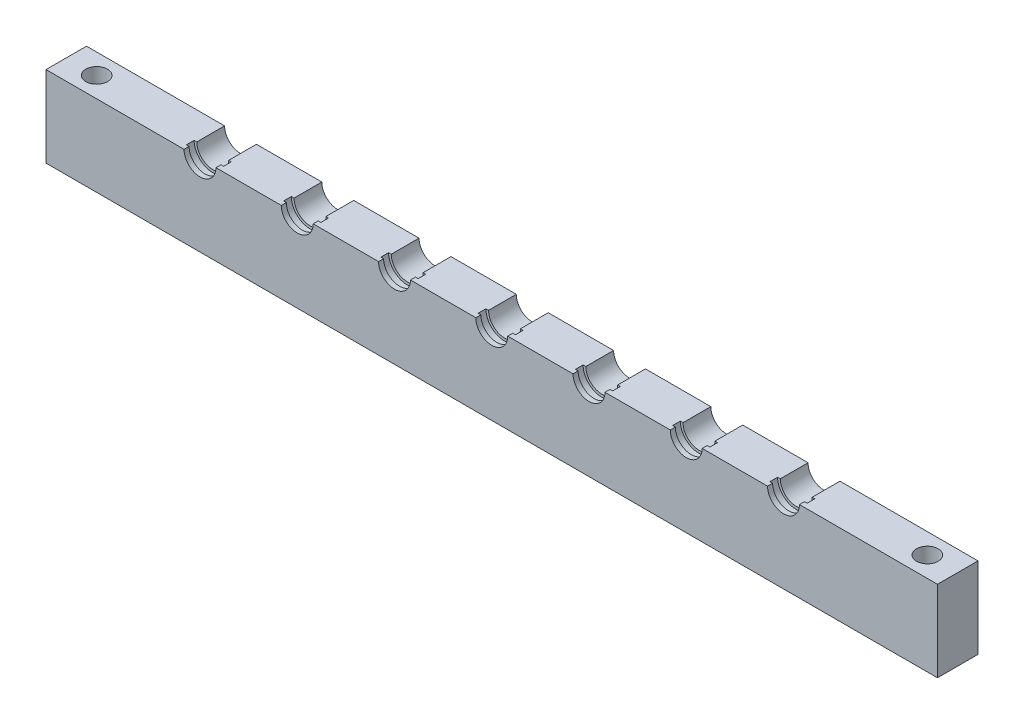
SolidWorks part; units mm, degrees
ref_plane "Front Plane" through (0, 0, 0) normal (0, 0, 1) x (1, 0, 0)
ref_plane "Top Plane" through (0, 0, 0) normal (0, 1, 0) x (1, 0, 0)
ref_plane "Right Plane" through (0, 0, 0) normal (1, 0, 0) x (0, 0, -1)
sketch "Sketch1" plane through (0, 0, 0) normal (0, 0, 1) x (1, 0, 0)
  line L1 (69.85, -6.35) -> (-69.85, -6.35)
  line L2 (69.85, -6.35) -> (69.85, 6.35)
  line L3 (69.85, 6.35) -> (-69.85, 6.35)
  line L4 (-69.85, -6.35) -> (-69.85, 6.35)
  line L5 (69.85, -6.35) -> (-69.85, 6.35) construction
  line L6 (69.85, 6.35) -> (-69.85, -6.35) construction
  point P0 (0, 0)
  dimension "D1" = 139.7
  dimension "D2" = 12.7
extrude "Boss-Extrude1" add sketch "Sketch1" along normal blind 6.35
hole_wizard "M3 Clearance Hole1" positions "Sketch3" profile "Sketch4" hole size "M3" standard "ANSI Metric" end condition through all
sketch "Sketch3" plane through (0, -6.35, 0) normal (0, -1, 0) x (-1, 0, 0)
  line L0 (69.85, -3.175) -> (-69.85, -3.175) construction
  line L1 (69.85, -6.35) -> (69.85, 0) construction
  line L2 (-69.85, -6.35) -> (-69.85, 0) construction
  point P9 (65.0875, -3.175)
  dimension "D1" = 4.7625
sketch "Sketch4" plane through (-65.0875, -6.35, 3.175) normal (1, 0, 0) x (0, 0, -1)
  line L0 (0, 0) -> (0, 12.7)
  line L1 (0, 12.7) -> (1.7, 12.7)
  line L2 (1.7, 12.7) -> (1.7, 0)
  line L5 (1.7, 0) -> (0, 0)
  line L11 (0, -6.35) -> (0, 107.95) construction
  dimension "Thru Hole Dia." = 3.4
  dimension "Thru Hole Depth" = 12.7
mirror "Mirror1" about plane through (0, 0, 0) normal (1, 0, 0) of "M3 Clearance Hole1"
sketch "Sketch9" plane through (0, 6.35, 0) normal (0, 1, 0) x (1, 0, 0)
  line L0 (2.5, -5.5563) -> (2.921, -5.5563) construction
  line L1 (2.5, -6.35) -> (2.5, -5.5563) construction
  line L2 (2.921, -5.5563) -> (2.921, -4.3498) construction
  line L3 (2.5, -4.3498) -> (2.921, -4.3498) construction
  line L4 (2.5, -4.3498) -> (2.5, 0) construction
  line L5 (2.5, -5.5563) -> (2.921, -5.5563)
  line L6 (2.5, -6.35) -> (2.5, -5.5563)
  line L7 (2.921, -5.5563) -> (2.921, -4.3498)
  line L8 (2.5, -4.3498) -> (2.921, -4.3498)
  line L9 (2.5, -4.3498) -> (2.5, 0)
  line L10 (0, 0) -> (0, -6.35) construction
  line L11 (69.85, 0) -> (-69.85, 0) construction
  line L12 (69.85, -6.35) -> (-69.85, -6.35) construction
  line L13 (2.5, -6.35) -> (0, -6.35)
  line L14 (2.5, 0) -> (0, 0)
  line L15 (0, 0) -> (0, -6.35)
revolve "Cut-Revolve1" cut sketch "Sketch9" angle 360 about L10
pattern_linear "LPattern1" count 4 spacing 15.24 along (-1, 0, 0) of "Cut-Revolve1"
pattern_linear "LPattern2" count 4 spacing 15.24 along (1, 0, 0) of "Cut-Revolve1"
